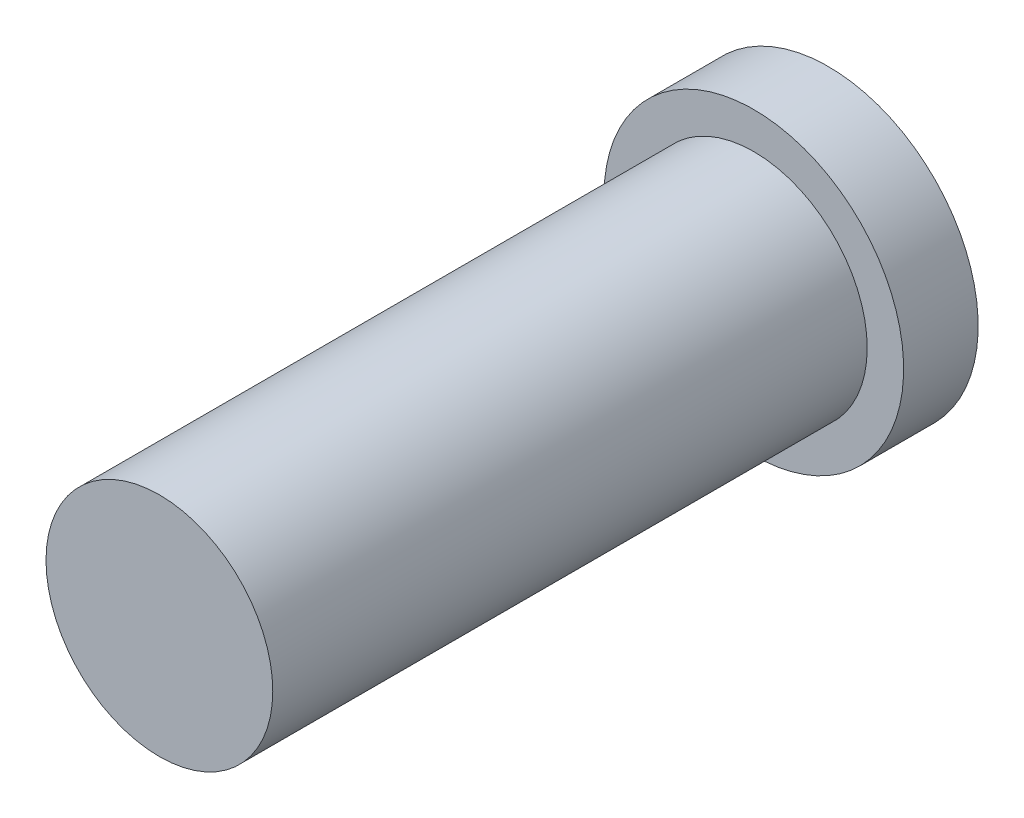
SolidWorks part; units mm, degrees
ref_plane "Front Plane" through (0, 0, 0) normal (0, 0, 1) x (1, 0, 0)
ref_plane "Top Plane" through (0, 0, 0) normal (0, 1, 0) x (1, 0, 0)
ref_plane "Right Plane" through (0, 0, 0) normal (1, 0, 0) x (0, 0, -1)
sketch "Sketch1" plane through (0, 0, 0) normal (0, 0, 1) x (1, 0, 0)
  circle A0 centre (0, 0) radius 0.7
extrude "Boss-Extrude1" add sketch "Sketch1" along normal blind 3.67
sketch "Sketch2" plane through (0, 0, 0) normal (0, 0, -1) x (-1, 0, 0)
  circle A0 centre (0, 0) radius 0.925
extrude "Boss-Extrude2" add sketch "Sketch2" along normal blind 0.46
sketch "Sketch3" plane through (0, 0, -0.46) normal (0, 0, -1) x (-1, 0, 0)
  circle A0 centre (0, 0) radius 0.455
extrude "Cut-Extrude1" cut sketch "Sketch3" against normal blind 3.5
